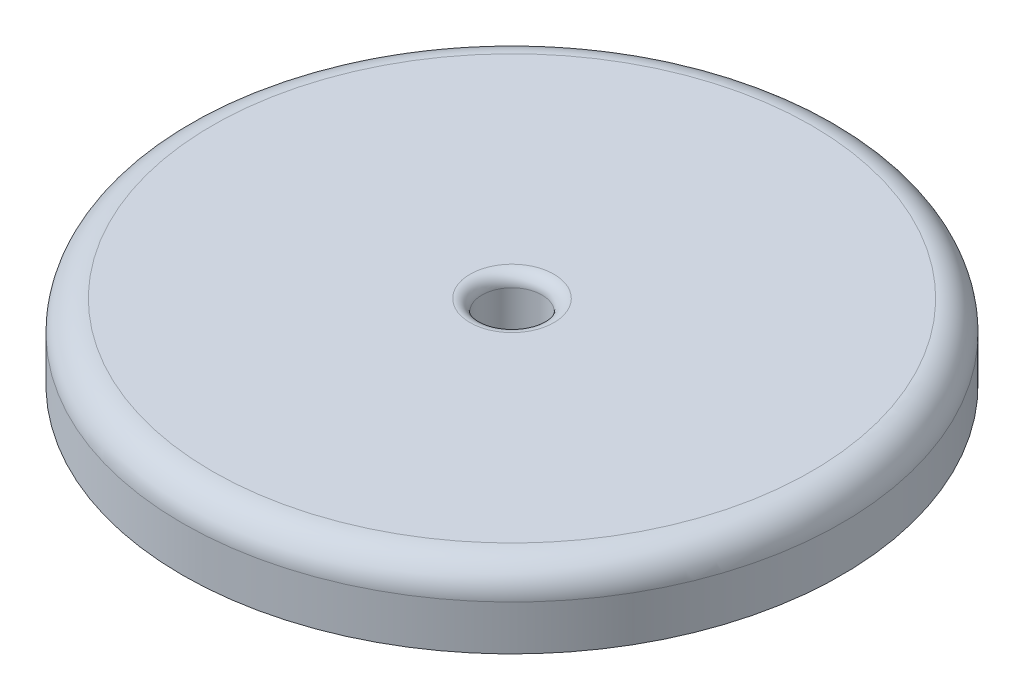
SolidWorks part; units mm, degrees
ref_plane "前视基准面" through (0, 0, 0) normal (0, 0, 1) x (1, 0, 0)
ref_plane "上视基准面" through (0, 0, 0) normal (0, 1, 0) x (1, 0, 0)
ref_plane "右视基准面" through (0, 0, 0) normal (1, 0, 0) x (0, 0, -1)
sketch "草图1" plane through (0, 0, 0) normal (0, 1, 0) x (1, 0, 0)
  circle A0 centre (0, 0) radius 11
  dimension "D1" = 22
extrude "凸台-拉伸1" add sketch "草图1" along normal blind 2.5
sketch "草图2" plane through (0, 2.5, 0) normal (0, 1, 0) x (1, 0, 0)
  circle A0 centre (0, 0) radius 1
  dimension "D1" = 2
extrude "切除-拉伸1" cut sketch "草图2" against normal through all
fillet "圆角1" radius 0.4 1 edges at (0, 2.5, 1)
fillet "圆角2" radius 1 1 edges at (0, 2.5, 11)
sketch "草图3" plane through (0, 0, 0) normal (0, -1, 0) x (1, 0, 0)
  circle A0 centre (0, 0) radius 1
  circle A1 centre (0, 0) radius 9.5
  dimension "D1" = 19
extrude "凸台-拉伸2" add sketch "草图3" along normal blind 0.5
fillet "圆角3" radius 0.2 2 edges at (0, 0, -9.5) (0, -0.5, -9.5)
